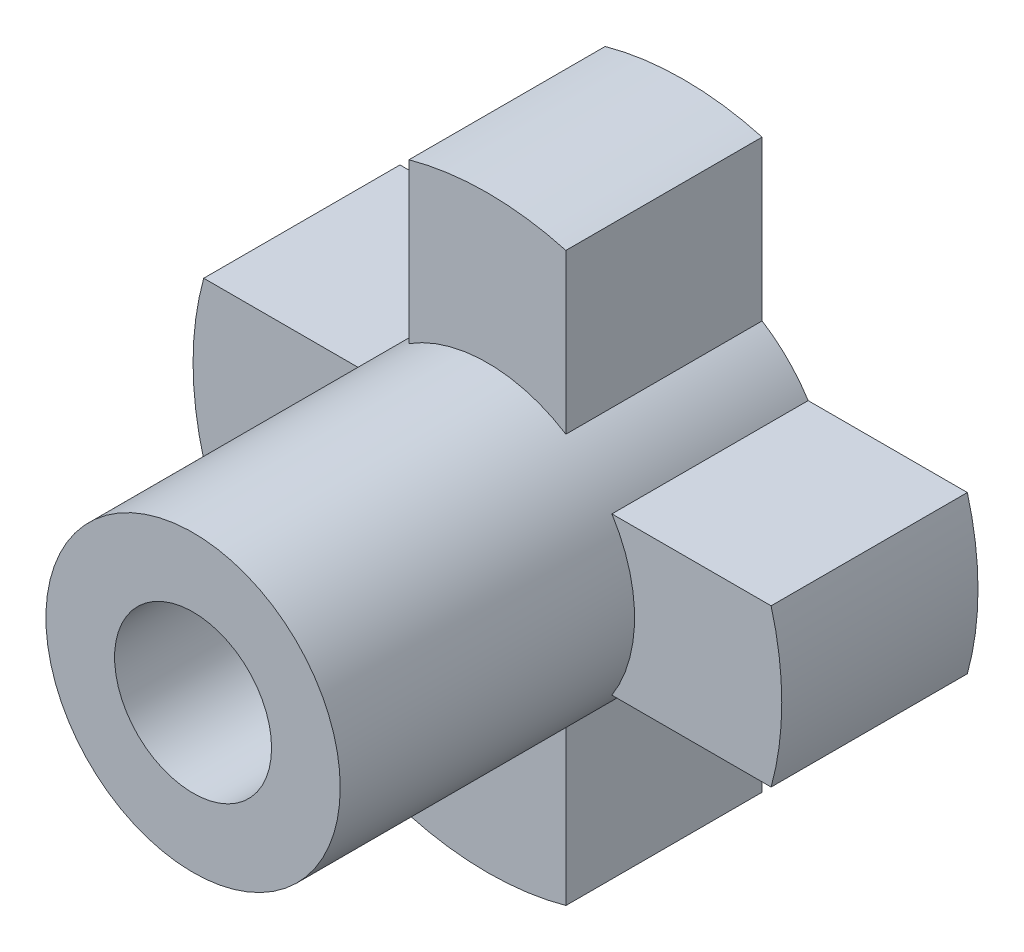
SolidWorks part; units mm, degrees
ref_plane "Plano frontal" through (0, 0, 0) normal (0, 0, 1) x (1, 0, 0)
ref_plane "Plano superior" through (0, 0, 0) normal (0, 1, 0) x (1, 0, 0)
ref_plane "Plano direito" through (0, 0, 0) normal (1, 0, 0) x (0, 0, -1)
sketch "Esboço1" plane through (0, 0, 0) normal (0, 0, 1) x (1, 0, 0)
  circle A0 centre (0, 0) radius 15
  dimension "D1" = 30
extrude "Ressalto-extrusão1" add sketch "Esboço1" along normal blind 10
sketch "Esboço2" plane through (0, 0, 10) normal (0, 0, 1) x (1, 0, 0)
  circle A0 centre (0, 0) radius 7.5
  dimension "D1" = 15
extrude "Ressalto-extrusão2" add sketch "Esboço2" along normal blind 15
sketch "Esboço3" plane through (0, 0, 25) normal (0, 0, 1) x (1, 0, 0)
  circle A0 centre (0, 0) radius 4
  dimension "D1" = 8
extrude "Corte-extrusão1" cut sketch "Esboço3" against normal blind 15
sketch "Esboço4" plane through (0, 0, 0) normal (0, 0, -1) x (-1, 0, 0)
  line L0 (-4, 6.3443) -> (-4, 14.4568)
  line L2 (4, -14.4568) -> (4, -6.3443)
  line L4 (-4, -14.4568) -> (-4, -6.3443)
  line L6 (-6.3443, -4) -> (-14.4568, -4)
  line L7 (14.4568, -4) -> (6.3443, -4)
  line L9 (14.4568, 4) -> (6.3443, 4)
  line L11 (-6.3443, 4) -> (-14.4568, 4)
  line L17 (4, 6.3443) -> (4, 14.4568)
  arc A0 (-6.3443, -4) -> (-4, -6.3443) centre (0, 0) ccw
  arc A1 (-4, 14.4568) -> (-14.4568, 4) centre (0, 0) ccw
  arc A2 (-14.4568, -4) -> (-4, -14.4568) centre (0, 0) ccw
  arc A3 (14.4568, 4) -> (4, 14.4568) centre (0, 0) ccw
  arc A4 (4, -14.4568) -> (14.4568, -4) centre (0, 0) ccw
  arc A5 (6.3443, 4) -> (4, 6.3443) centre (0, 0) ccw
  arc A6 (-4, 6.3443) -> (-6.3443, 4) centre (0, 0) ccw
  arc A7 (4, -6.3443) -> (6.3443, -4) centre (0, 0) ccw
  dimension "D1" = 15
extrude "Corte-extrusão2" cut sketch "Esboço4" against normal blind 20
sketch "Esboço5" plane through (0, 0, 0) normal (1, 0, 0) x (0, 0, -1)
  line L0 (6.6535, 0) -> (-30.3304, 0) construction
  circle A0 centre (-13.004, 0) radius 1.5
  dimension "D1" = 3
extrude "Corte-extrusão3" cut sketch "Esboço5" against normal blind 20
